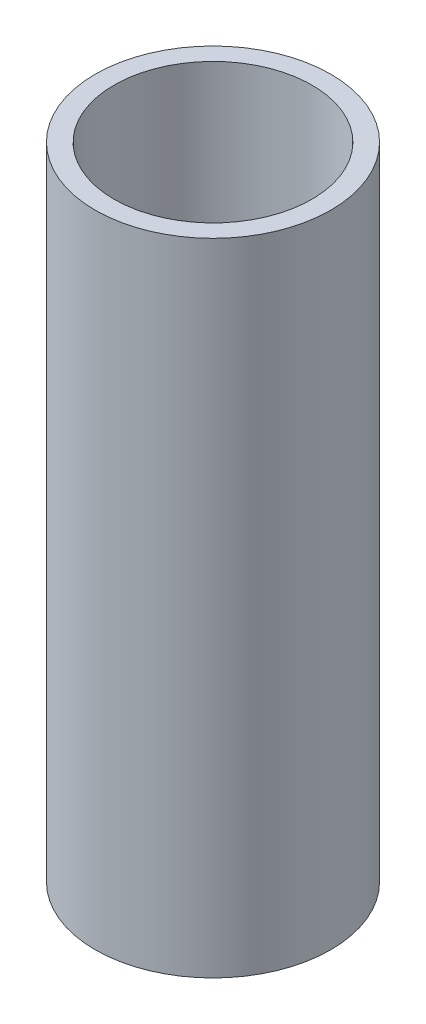
SolidWorks part; units mm, degrees
material "AISI 304"
ref_plane "前视基准面" through (0, 0, 0) normal (0, 0, 1) x (1, 0, 0)
ref_plane "上视基准面" through (0, 0, 0) normal (0, 1, 0) x (1, 0, 0)
ref_plane "右视基准面" through (0, 0, 0) normal (1, 0, 0) x (0, 0, -1)
other "Configuration Table"
sketch "草图1" plane through (0, 0, 0) normal (0, 1, 0) x (1, 0, 0)
  circle A0 centre (0, 0) radius 4.2
  circle A1 centre (0, 0) radius 5
  dimension "D1" = 8.4
  dimension "D2" = 10
extrude "凸台-拉伸1" add sketch "草图1" along normal blind 27.19
